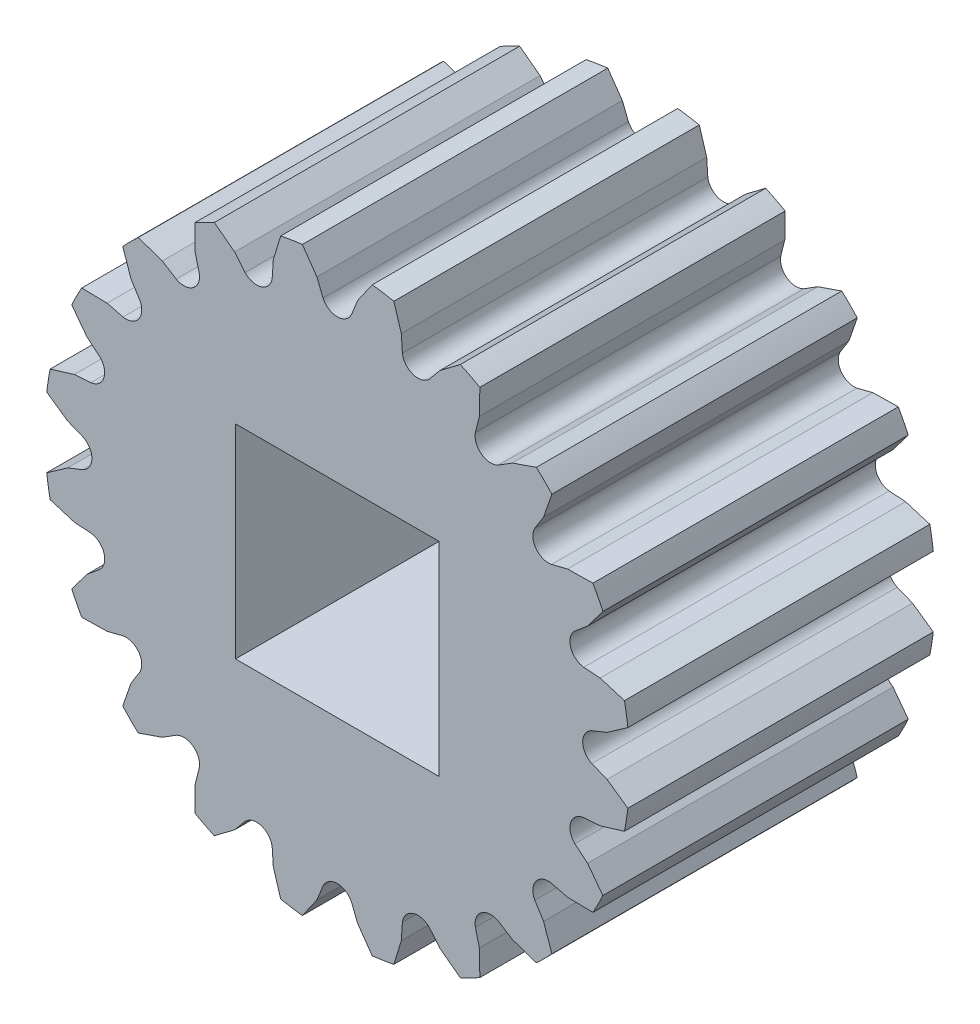
SolidWorks part; units mm, degrees
ref_plane "Plan de face" through (0, 0, 0) normal (0, 0, 1) x (1, 0, 0)
ref_plane "Plan de dessus" through (0, 0, 0) normal (0, 1, 0) x (1, 0, 0)
ref_plane "Plan de droite" through (0, 0, 0) normal (1, 0, 0) x (0, 0, -1)
sketch "Sketch1" plane through (0, 0, 0) normal (0, 0, 1) x (1, 0, 0)
  line L1 (-4, 4) -> (4, 4)
  line L2 (-4, 4) -> (-4, -4)
  line L3 (-4, -4) -> (4, -4)
  line L4 (4, 4) -> (4, -4)
  line L5 (-4, 4) -> (4, -4) construction
  line L6 (-4, -4) -> (4, 4) construction
  circle A0 centre (0, 0) radius 11.5
  dimension "D3" = 23
  dimension "D1" = 8
  dimension "D2" = 8
extrude "Boss-Extrude1" add sketch "Sketch1" along normal blind 12
sketch "Sketch2" plane through (0, 0, 12) normal (0, 0, 1) x (1, 0, 0)
  line L0 (0, 11.6) -> (1.5, 11.6)
  line L1 (0, 10.6) -> (0, 11.6) construction
  line L2 (0, 10) -> (0.5593, 10) construction
  line L3 (0, 10) -> (-0.5593, 10) construction
  line L4 (0, 11.6) -> (-1.5, 11.6)
  line L5 (-1.5, 11.6) -> (-0.8, 10.6)
  line L6 (-0.8, 10.6) -> (-0.5593, 10)
  line L7 (-0.8, 10.6) -> (0, 10.6) construction
  line L8 (0, 10.6) -> (0.8, 10.6) construction
  line L9 (1.5, 11.6) -> (0.8, 10.6)
  line L10 (0.8, 10.6) -> (0.5593, 10)
  line L11 (0, 10.6) -> (0, 10) construction
  arc A0 (-0.5593, 10) -> (0.5593, 10) centre (0, 10.2587) ccw
  point P10 (0, 0)
  dimension "D1" = 1.5
  dimension "D2" = 0.8
  dimension "D3" = 1
  dimension "D4" = 0.6
  dimension "D5" = 10
extrude "Cut-Extrude1" cut sketch "Sketch2" against normal blind 12
pattern_circular "CirPattern1" count 20 over 360 about axis through (0, 0, 0) along (0, 0, 1) of "Cut-Extrude1"
sketch "Sketch3" plane through (0, 0, 12) normal (0, 0, 1) x (1, 0, 0)
  circle A0 centre (0, 0) radius 7.649
